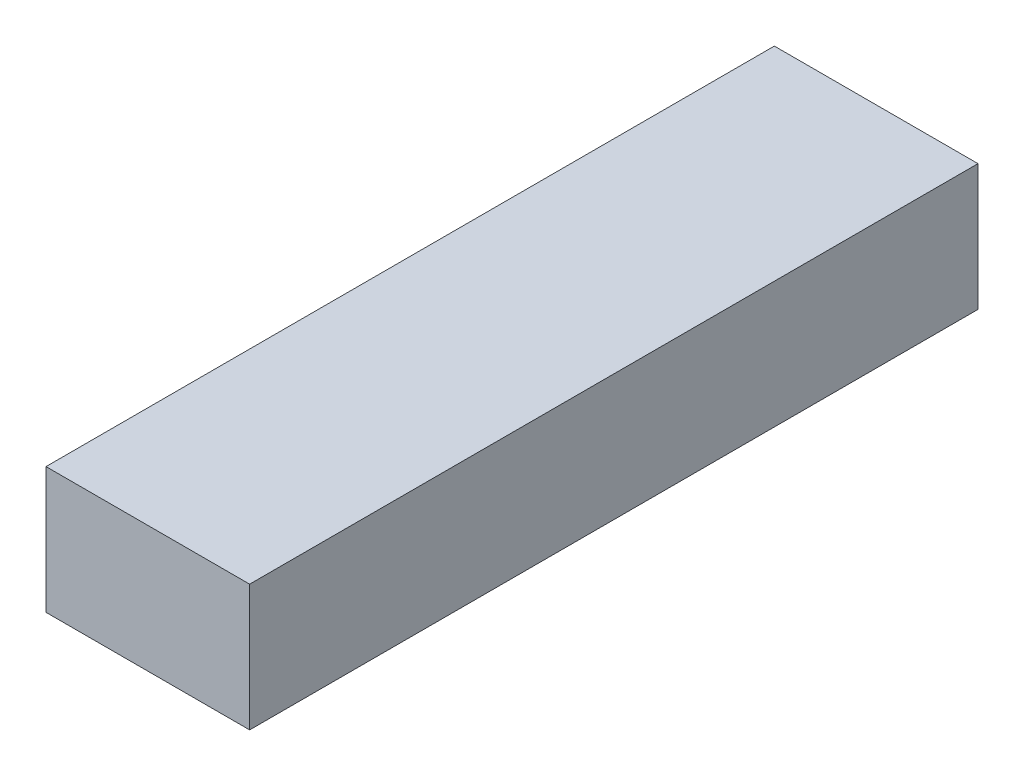
SolidWorks part; units mm, degrees
ref_plane "정면" through (0, 0, 0) normal (0, 0, 1) x (1, 0, 0)
ref_plane "윗면" through (0, 0, 0) normal (0, 1, 0) x (1, 0, 0)
ref_plane "우측면" through (0, 0, 0) normal (1, 0, 0) x (0, 0, -1)
sketch "스케치2" plane through (0, 0, 44.2) normal (0, 0, -1) x (-1, 0, 0)
  line L0 (63.4142, 33.848) -> (63.4142, 74.748) construction
  line L1 (105.1142, 33.848) -> (71.5642, 33.848)
  line L2 (105.1142, 33.848) -> (105.1142, 54.648)
  line L3 (105.1142, 54.648) -> (71.5642, 54.648)
  line L4 (71.5642, 33.848) -> (71.5642, 54.648)
  dimension "D1" = 20.8
  dimension "D2" = 8.15
extrude "보스-돌출2" add sketch "스케치2" along normal blind 120
